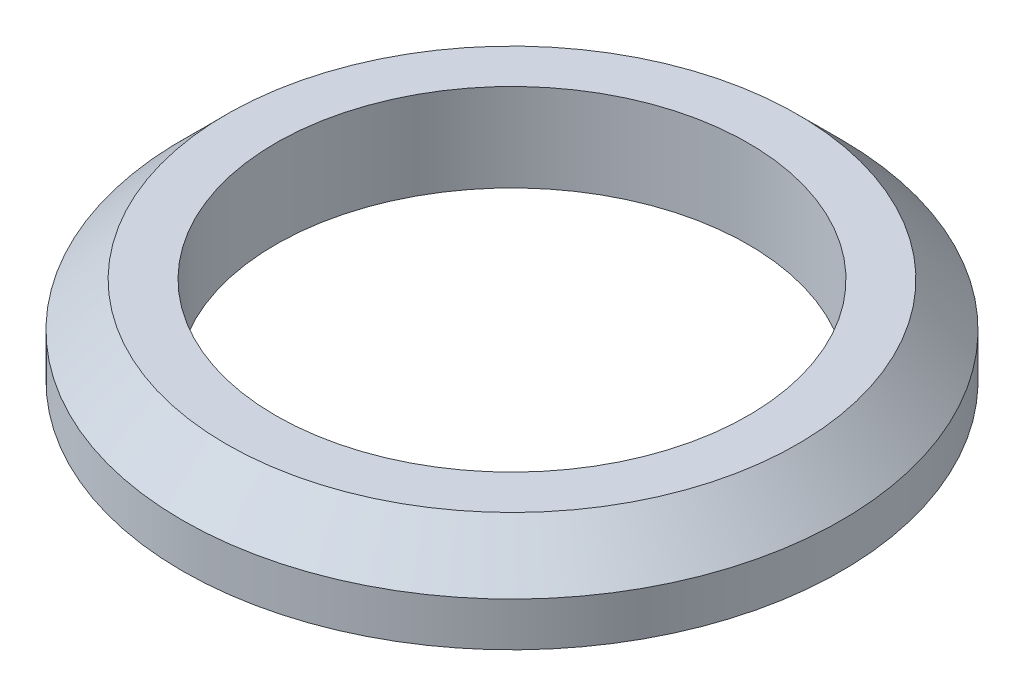
SolidWorks part; units mm, degrees
ref_plane "Front Plane" through (0, 0, 0) normal (0, 0, 1) x (1, 0, 0)
ref_plane "Top Plane" through (0, 0, 0) normal (0, 1, 0) x (1, 0, 0)
ref_plane "Right Plane" through (0, 0, 0) normal (1, 0, 0) x (0, 0, -1)
sketch "Sketch1" plane through (0, 0, 0) normal (0, 1, 0) x (1, 0, 0)
  circle A0 centre (0, 0) radius 2.15
  circle A1 centre (0, 0) radius 3
  dimension "D1" = 4.3
  dimension "D2" = 6
extrude "Boss-Extrude1" add sketch "Sketch1" along normal blind 0.8
chamfer "Chamfer1" distance 0.4 angle 45 1 edges at (0, 0.8, 3)
